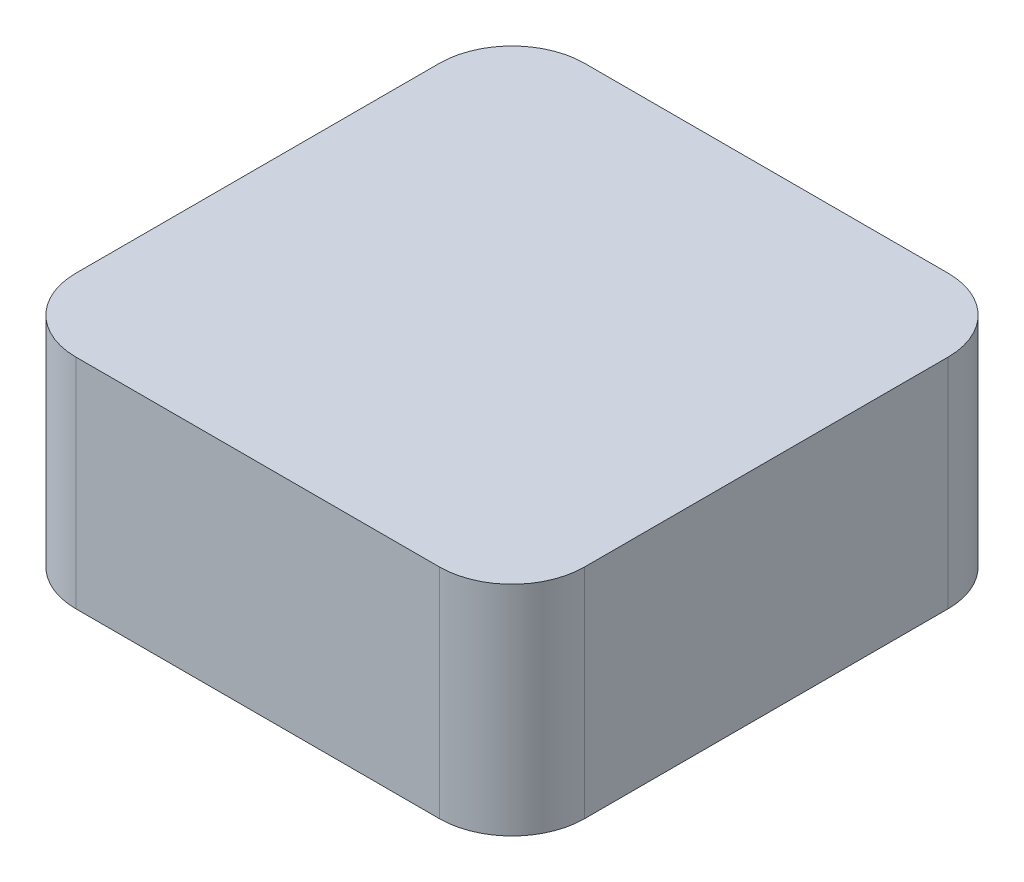
SolidWorks part; units mm, degrees
ref_plane "Front Plane" through (0, 0, 0) normal (0, 0, 1) x (1, 0, 0)
ref_plane "Top Plane" through (0, 0, 0) normal (0, 1, 0) x (1, 0, 0)
ref_plane "Right Plane" through (0, 0, 0) normal (1, 0, 0) x (0, 0, -1)
sketch "Sketch1" plane through (0, 0, 0) normal (0, 1, 0) x (1, 0, 0)
  line L1 (-31.75, -44.45) -> (31.75, -44.45)
  line L2 (-44.45, -31.75) -> (-44.45, 31.75)
  line L3 (-31.75, 44.45) -> (31.75, 44.45)
  line L4 (44.45, -31.75) -> (44.45, 31.75)
  line L5 (-44.45, -44.45) -> (44.45, 44.45) construction
  line L6 (-44.45, 44.45) -> (44.45, -44.45) construction
  arc A0 (31.75, 44.45) -> (44.45, 31.75) centre (31.75, 31.75) cw
  arc A1 (31.75, -44.45) -> (44.45, -31.75) centre (31.75, -31.75) ccw
  arc A2 (-31.75, -44.45) -> (-44.45, -31.75) centre (-31.75, -31.75) cw
  arc A3 (-44.45, 31.75) -> (-31.75, 44.45) centre (-31.75, 31.75) cw
  point P0 (0, 0)
  dimension "D3" = 12.7
  dimension "D1" = 88.9
extrude "Boss-Extrude1" add sketch "Sketch1" along normal blind 38.1
